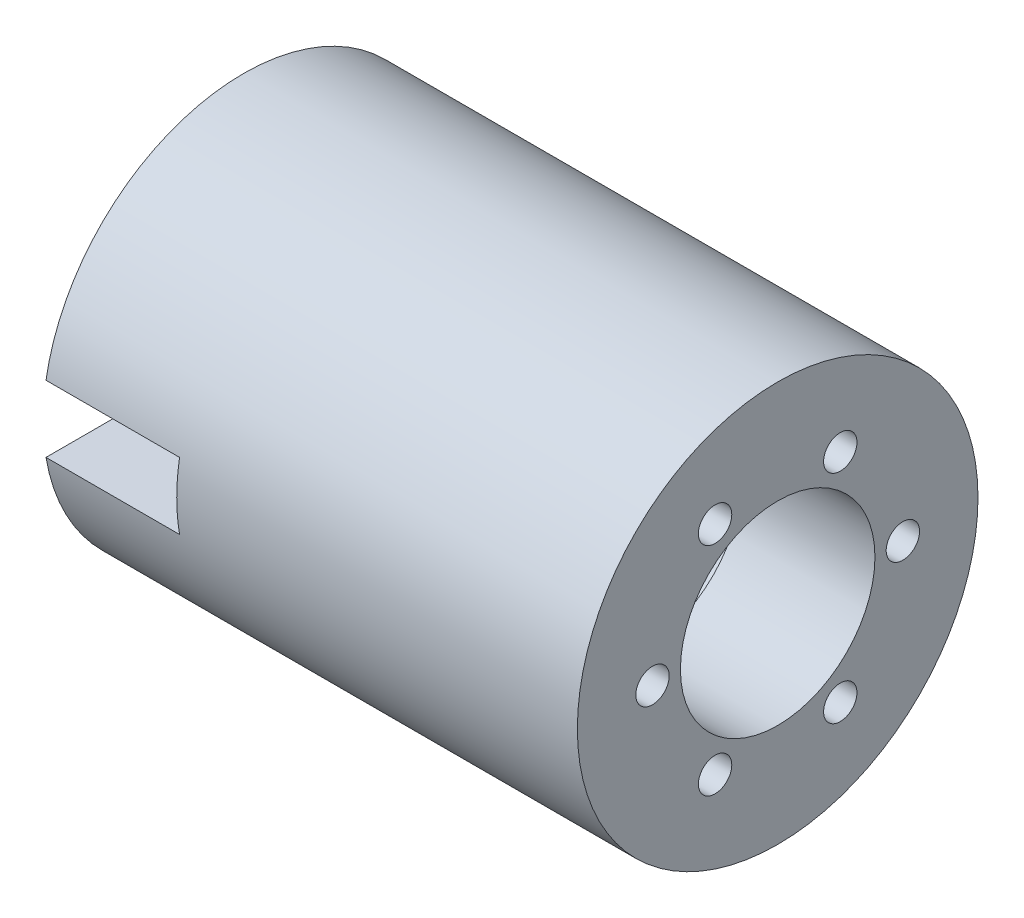
SolidWorks part; units mm, degrees
ref_plane "Front Plane" through (0, 0, 0) normal (0, 0, 1) x (1, 0, 0)
ref_plane "Top Plane" through (0, 0, 0) normal (0, 1, 0) x (1, 0, 0)
ref_plane "Right Plane" through (0, 0, 0) normal (1, 0, 0) x (0, 0, -1)
sketch "Sketch1" plane through (0, 0, 0) normal (0, 0, 1) x (1, 0, 0)
  line L0 (-50.8, 0) -> (50.8, 0) construction
  line L1 (0, 0) -> (0, 21.2725) construction
  line L2 (-50.8, 21.2725) -> (50.8, 21.2725)
  line L3 (-50.8, 21.2725) -> (-50.8, 38.1)
  line L4 (-50.8, 38.1) -> (44.45, 38.1)
  line L5 (44.45, 38.1) -> (44.45, 76.2)
  line L6 (44.45, 76.2) -> (50.8, 76.2)
  line L7 (50.8, 76.2) -> (50.8, 21.2725)
  line L8 (44.45, 38.1) -> (50.8, 38.1)
  line L9 (25.4, 21.2725) -> (25.4, 15.875)
  line L10 (25.4, 15.875) -> (50.8, 15.875)
  line L11 (50.8, 15.875) -> (50.8, 21.2725)
  point P4 (0, 0)
  point P10 (0, 21.2725)
  dimension "D1" = 6.35
  dimension "D2" = 21.2725
  dimension "D3" = 101.6
  dimension "D4" = 76.2
  dimension "D5" = 38.1
  dimension "D6" = 25.4
  dimension "D7" = 15.875
revolve "Revolve1" add sketch "Sketch1" angle 360 about L0
sketch "Sketch2" plane through (50.8, 0, 0) normal (1, 0, 0) x (0, 0, -1)
  line L0 (-9.316, 41.6349) -> (-4.7427, 53.3559)
  line L1 (31.3989, 28.8853) -> (43.8362, 30.7853)
  line L2 (40.7149, -12.7495) -> (48.5789, -22.5706)
  line L3 (9.316, -41.6349) -> (4.7427, -53.3559)
  line L4 (-31.3989, -28.8853) -> (-43.8362, -30.7853)
  line L5 (-40.7149, 12.7495) -> (-48.5789, 22.5706)
  circle A0 centre (0, 0) radius 80
  circle A1 centre (0, 68) radius 2.5
  circle A2 centre (8.3322, 73.5294) radius 2.5
  circle A3 centre (17.5997, 65.683) radius 2.5
  circle A4 centre (27.0791, 68.8674) radius 2.5
  circle A5 centre (34, 58.8897) radius 2.5
  circle A6 centre (43.9806, 59.5122) radius 2.5
  circle A7 centre (48.0833, 48.0833) radius 2.5
  circle A8 centre (57.8849, 46.1014) radius 2.5
  circle A9 centre (58.8897, 34) radius 2.5
  circle A10 centre (67.8444, 29.5488) radius 2.5
  circle A11 centre (65.683, 17.5997) radius 2.5
  circle A12 centre (73.1805, 10.9825) radius 2.5
  circle A13 centre (68, 0) radius 2.5
  circle A14 centre (73.5294, -8.3322) radius 2.5
  circle A15 centre (65.683, -17.5997) radius 2.5
  circle A16 centre (68.8674, -27.0791) radius 2.5
  circle A17 centre (58.8897, -34) radius 2.5
  circle A18 centre (59.5122, -43.9806) radius 2.5
  circle A19 centre (48.0833, -48.0833) radius 2.5
  circle A20 centre (46.1014, -57.8849) radius 2.5
  circle A21 centre (34, -58.8897) radius 2.5
  circle A22 centre (29.5488, -67.8444) radius 2.5
  circle A23 centre (17.5997, -65.683) radius 2.5
  circle A24 centre (10.9825, -73.1805) radius 2.5
  circle A25 centre (0, -68) radius 2.5
  circle A26 centre (-8.3322, -73.5294) radius 2.5
  circle A27 centre (-17.5997, -65.683) radius 2.5
  circle A28 centre (-27.0791, -68.8674) radius 2.5
  circle A29 centre (-34, -58.8897) radius 2.5
  circle A30 centre (-43.9806, -59.5122) radius 2.5
  circle A31 centre (-48.0833, -48.0833) radius 2.5
  circle A32 centre (-57.8849, -46.1014) radius 2.5
  circle A33 centre (-58.8897, -34) radius 2.5
  circle A34 centre (-67.8444, -29.5488) radius 2.5
  circle A35 centre (-65.683, -17.5997) radius 2.5
  circle A36 centre (-73.1805, -10.9825) radius 2.5
  circle A37 centre (-68, 0) radius 2.5
  circle A38 centre (-73.5294, 8.3322) radius 2.5
  circle A39 centre (-65.683, 17.5997) radius 2.5
  circle A40 centre (-68.8674, 27.0791) radius 2.5
  circle A41 centre (-58.8897, 34) radius 2.5
  circle A42 centre (-59.5122, 43.9806) radius 2.5
  circle A43 centre (-48.0833, 48.0833) radius 2.5
  circle A44 centre (-46.1014, 57.8849) radius 2.5
  circle A45 centre (-34, 58.8897) radius 2.5
  circle A46 centre (-29.5488, 67.8444) radius 2.5
  circle A47 centre (-17.5997, 65.683) radius 2.5
  circle A48 centre (-10.9825, 73.1805) radius 2.5
  circle A49 centre (0, 0) radius 18.5
  circle A50 centre (-11.9063, 20.6222) radius 3.175
  circle A51 centre (11.9063, 20.6222) radius 3.175
  circle A52 centre (23.8125, 0) radius 3.175
  circle A53 centre (11.9063, -20.6222) radius 3.175
  circle A54 centre (-11.9063, -20.6222) radius 3.175
  spline S0 degree 2 poles (5.9532, 60.7088) (27.9941, 58.3228) (43.6425, 42.6185) knots 0 0 0 1 1 1
  spline S1 degree 2 poles (4.0813, 28.8708) (21.9975, 36.8421) (41.5951, 37.5241) knots 0 0 0 1 1 1
  spline S2 degree 1 poles (-10, 38) (-9.316, 41.6349) knots 0 0 1 1
  spline S3 degree 3 poles (-4.7427, 53.3559) (-3.6172, 58.1411) (1.3644, 61.1789) (5.9532, 60.7088) knots 0 0 0 0 1 1 1 1
  spline S4 degree 3 poles (4.0813, 28.8708) (-1.8873, 26.0232) (-10.3042, 30.435) (-10, 38) knots 0 0 0 0 1 1 1 1
  spline S5 degree 2 poles (41.5951, 37.5241) (45.9407, 38.7363) (43.6425, 42.6185) knots 0 0 0 1 1 1
  spline S6 degree 2 poles (53.2944, -17.2603) (56.5169, -20.4176) (58.7299, -16.4862) knots 0 0 0 1 1 1
  spline S7 degree 2 poles (55.552, 25.1988) (64.506, 4.9178) (58.7299, -16.4862) knots 0 0 0 1 1 1
  spline S8 degree 3 poles (43.8362, 30.7853) (48.5431, 32.2031) (53.6647, 29.4078) (55.552, 25.1988) knots 0 0 0 0 1 1 1 1
  spline S9 degree 1 poles (27.909, 27.6603) (31.3989, 28.8853) knots 0 0 1 1
  spline S10 degree 3 poles (27.0435, 10.9008) (21.5931, 14.646) (21.2054, 24.1412) (27.909, 27.6603) knots 0 0 0 0 1 1 1 1
  spline S11 degree 2 poles (27.0435, 10.9008) (42.905, -0.6293) (53.2944, -17.2603) knots 0 0 0 1 1 1
  spline S12 degree 2 poles (11.6993, -54.7845) (10.5763, -59.1539) (15.0875, -59.1047) knots 0 0 0 1 1 1
  spline S13 degree 2 poles (49.5988, -35.51) (36.5119, -53.405) (15.0875, -59.1047) knots 0 0 0 1 1 1
  spline S14 degree 3 poles (48.5789, -22.5706) (52.1602, -25.938) (52.3003, -31.7711) (49.5988, -35.51) knots 0 0 0 0 1 1 1 1
  spline S15 degree 1 poles (37.909, -10.3397) (40.7149, -12.7495) knots 0 0 1 1
  spline S16 degree 3 poles (22.9622, -17.9699) (23.4804, -11.3771) (31.5096, -6.2938) (37.909, -10.3397) knots 0 0 0 0 1 1 1 1
  spline S17 degree 2 poles (22.9622, -17.9699) (20.9075, -37.4715) (11.6993, -54.7845) knots 0 0 0 1 1 1
  spline S18 degree 2 poles (-41.5951, -37.5241) (-45.9407, -38.7363) (-43.6425, -42.6185) knots 0 0 0 1 1 1
  spline S19 degree 2 poles (-5.9532, -60.7088) (-27.9941, -58.3228) (-43.6425, -42.6185) knots 0 0 0 1 1 1
  spline S20 degree 3 poles (4.7427, -53.3559) (3.6172, -58.1411) (-1.3644, -61.1789) (-5.9532, -60.7088) knots 0 0 0 0 1 1 1 1
  spline S21 degree 1 poles (10, -38) (9.316, -41.6349) knots 0 0 1 1
  spline S22 degree 3 poles (-4.0813, -28.8708) (1.8873, -26.0232) (10.3042, -30.435) (10, -38) knots 0 0 0 0 1 1 1 1
  spline S23 degree 2 poles (-4.0813, -28.8708) (-21.9975, -36.8421) (-41.5951, -37.5241) knots 0 0 0 1 1 1
  spline S24 degree 2 poles (-53.2944, 17.2603) (-56.5169, 20.4176) (-58.7299, 16.4862) knots 0 0 0 1 1 1
  spline S25 degree 2 poles (-55.552, -25.1988) (-64.506, -4.9178) (-58.7299, 16.4862) knots 0 0 0 1 1 1
  spline S26 degree 3 poles (-43.8362, -30.7853) (-48.5431, -32.2031) (-53.6647, -29.4078) (-55.552, -25.1988) knots 0 0 0 0 1 1 1 1
  spline S27 degree 1 poles (-27.909, -27.6603) (-31.3989, -28.8853) knots 0 0 1 1
  spline S28 degree 3 poles (-27.0435, -10.9008) (-21.5931, -14.646) (-21.2054, -24.1412) (-27.909, -27.6603) knots 0 0 0 0 1 1 1 1
  spline S29 degree 2 poles (-27.0435, -10.9008) (-42.905, 0.6293) (-53.2944, 17.2603) knots 0 0 0 1 1 1
  spline S30 degree 2 poles (-11.6993, 54.7845) (-10.5763, 59.1539) (-15.0875, 59.1047) knots 0 0 0 1 1 1
  spline S31 degree 2 poles (-49.5988, 35.51) (-36.5119, 53.405) (-15.0875, 59.1047) knots 0 0 0 1 1 1
  spline S32 degree 3 poles (-48.5789, 22.5706) (-52.1602, 25.938) (-52.3003, 31.7711) (-49.5988, 35.51) knots 0 0 0 0 1 1 1 1
  spline S33 degree 1 poles (-37.909, 10.3397) (-40.7149, 12.7495) knots 0 0 1 1
  spline S34 degree 3 poles (-22.9622, 17.9699) (-23.4804, 11.3771) (-31.5096, 6.2938) (-37.909, 10.3397) knots 0 0 0 0 1 1 1 1
  spline S35 degree 2 poles (-22.9622, 17.9699) (-20.9075, 37.4715) (-11.6993, 54.7845) knots 0 0 0 1 1 1
extrude "Cut-Extrude1" cut sketch "Sketch2" against normal blind 25.4 contours A54 | A53 | A52 | A51 | A50 | A49
pattern_circular "CirPattern1" count 6 over 360 about axis through (-50.8, 0, 0) along (-1, 0, 0) of "Cut-Extrude1"
sketch "Sketch3" plane through (0, 0, 0) normal (0, 0, 1) x (1, 0, 0)
  line L0 (0, 0) -> (-50.8, 0) construction
  line L1 (-50.8, 38.1) -> (-50.8, -38.1) construction
  line L2 (-50.8, -6.35) -> (-50.8, 6.35)
  line L3 (-50.8, 6.35) -> (-25.4, 6.35)
  line L4 (-25.4, 6.35) -> (-25.4, -6.35)
  line L5 (-25.4, -6.35) -> (-50.8, -6.35)
  point P8 (-50.8, 0)
  dimension "D1" = 12.7
  dimension "D2" = 25.4
extrude "Cut-Extrude2" cut sketch "Sketch3" along normal through all
